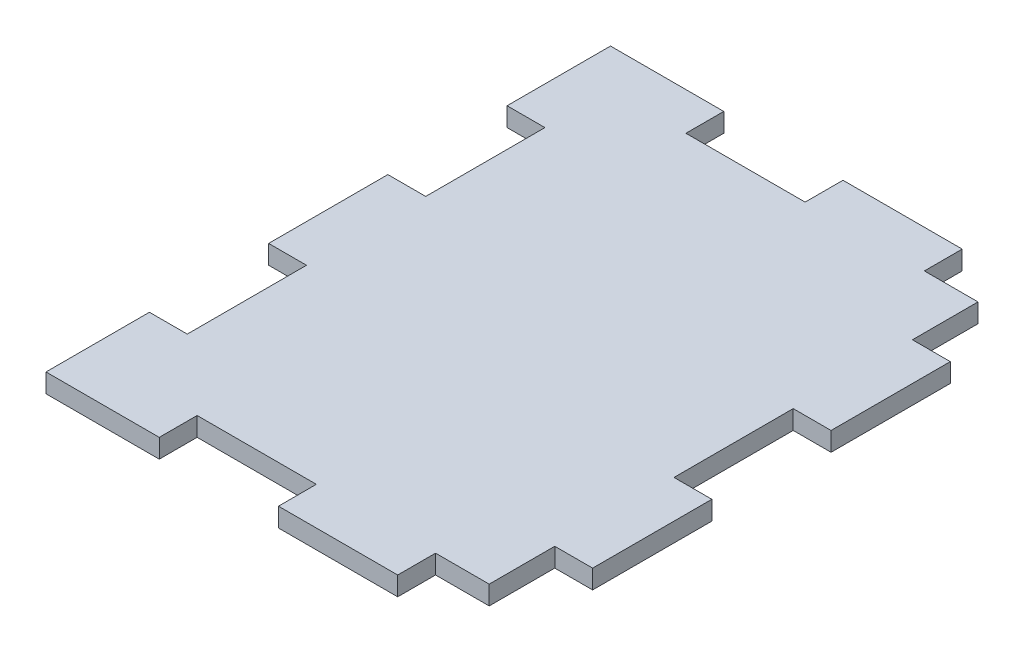
SolidWorks part; units mm, degrees
ref_plane "Front Plane" through (0, 0, 0) normal (0, 0, 1) x (1, 0, 0)
ref_plane "Top Plane" through (0, 0, 0) normal (0, 1, 0) x (1, 0, 0)
ref_plane "Right Plane" through (0, 0, 0) normal (1, 0, 0) x (0, 0, -1)
sketch "Sketch1" plane through (0, 0, 0) normal (0, 1, 0) x (1, 0, 0)
  line L1 (0, 0) -> (37.175, 0)
  line L2 (0, 0) -> (0, 47.35)
  line L3 (0, 47.35) -> (37.175, 47.35)
  line L4 (37.175, 0) -> (37.175, 47.35)
  dimension "D1" = 37.175
  dimension "D2" = 47.35
extrude "Boss-Extrude1" add sketch "Sketch1" along normal blind 1.5875
sketch "Sketch2" plane through (0, 1.5875, 0) normal (0, 1, 0) x (1, 0, 0)
  line L0 (0, 47.35) -> (0, 0) construction
  line L1 (3.175, 38.675) -> (0, 38.675)
  line L2 (3.175, 38.675) -> (3.175, 28.675)
  line L3 (3.175, 28.675) -> (0, 28.675)
  line L4 (0, 38.675) -> (0, 28.675)
  line L5 (37.175, 0) -> (37.175, 47.35) construction
  line L6 (3.175, 18.675) -> (0, 18.675)
  line L7 (3.175, 18.675) -> (3.175, 8.675)
  line L8 (3.175, 8.675) -> (0, 8.675)
  line L9 (0, 18.675) -> (0, 8.675)
  line L10 (34, 18.675) -> (37.175, 18.675)
  line L11 (34, 38.675) -> (34, 44.175)
  line L12 (34, 8.675) -> (37.175, 8.675)
  line L13 (37.175, 38.675) -> (37.175, 47.35)
  line L14 (37.175, 47.35) -> (0, 47.35) construction
  line L15 (34, 28.675) -> (37.175, 28.675)
  line L16 (37.175, 28.675) -> (37.175, 18.675)
  line L17 (34, 38.675) -> (37.175, 38.675)
  line L18 (34, 28.675) -> (34, 18.675)
  line L19 (29.5, 44.175) -> (34, 44.175)
  line L20 (29.5, 44.175) -> (29.5, 47.35)
  line L21 (29.5, 47.35) -> (37.175, 47.35)
  line L23 (19.5, 44.175) -> (9.5, 44.175)
  line L24 (19.5, 44.175) -> (19.5, 47.35)
  line L25 (19.5, 47.35) -> (9.5, 47.35)
  line L26 (9.5, 44.175) -> (9.5, 47.35)
  line L27 (29.5, 3.175) -> (37.175, 3.175)
  line L28 (29.5, 3.175) -> (29.5, 0)
  line L29 (29.5, 0) -> (37.175, 0)
  line L30 (37.175, 3.175) -> (37.175, 0)
  line L31 (19.5, 3.175) -> (9.5, 3.175)
  line L32 (19.5, 3.175) -> (19.5, 0)
  line L33 (19.5, 0) -> (9.5, 0)
  line L34 (9.5, 3.175) -> (9.5, 0)
  line L35 (37.175, 47.35) -> (0, 47.35) construction
  line L36 (0, 47.35) -> (0, 0) construction
  line L37 (37.175, 8.675) -> (37.175, 3.175)
  line L38 (34, 8.675) -> (34, 3.175)
  line M28 (0, 47.35) -> (0, 0)
  line M29 (0, 0) -> (37.175, 0)
  line M30 (37.175, 0) -> (37.175, 47.35)
  line M31 (37.175, 47.35) -> (0, 47.35)
  dimension "D1" = 10
  dimension "D2" = 10
  dimension "D3" = 8.675
  dimension "D4" = 41
  dimension "D5" = 9.5
  dimension "D6" = 10
  dimension "D7" = 3.175
  dimension "D8" = 10
extrude "Cut-Extrude1" cut sketch "Sketch2" against normal through all contours L20 L19 L11 L17 M30 M31 | L15 L18 L10 M30 | L27 L28 M29 M30 | L12 L38 L27 M30 | L31 L34 L32 M29 | L8 L7 L6 M28 | L3 L2 L1 M28 | L26 L23 L24 M31
